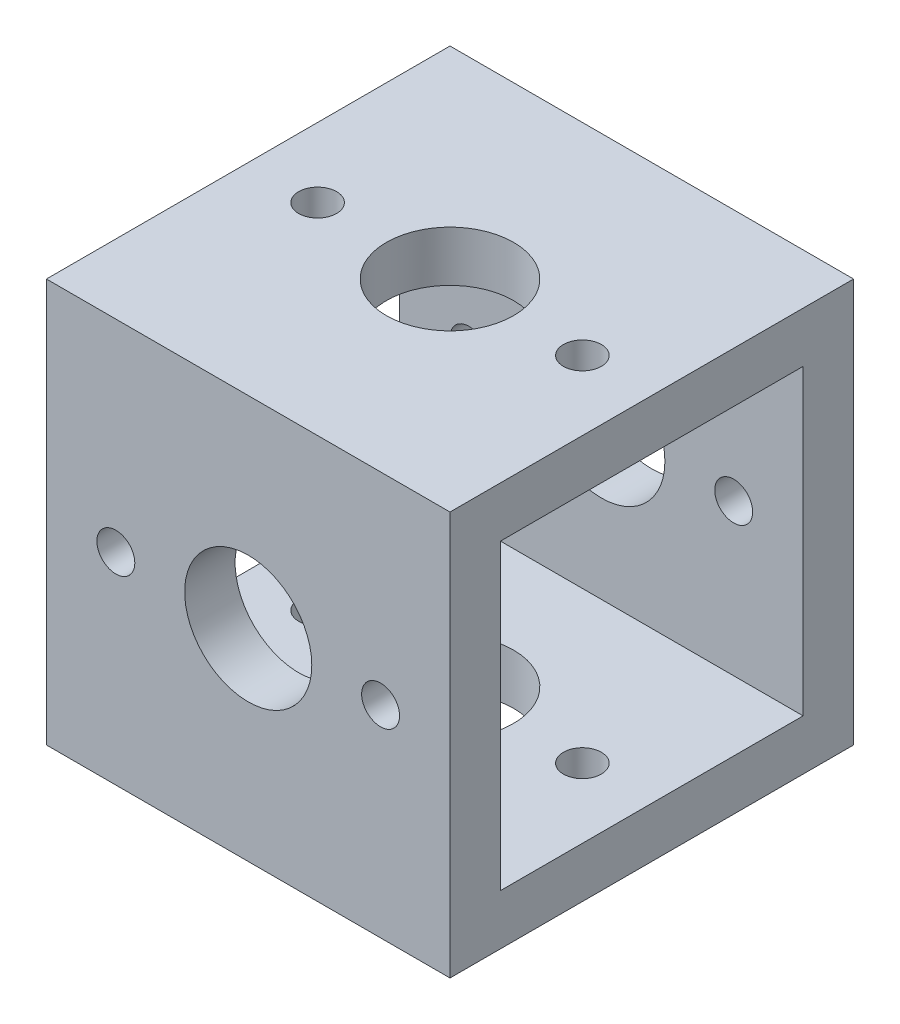
SolidWorks part; units mm, degrees
ref_plane "Front" through (0, 0, 0) normal (0, 0, 1) x (1, 0, 0)
ref_plane "Top" through (0, 0, 0) normal (0, 1, 0) x (1, 0, 0)
ref_plane "Right" through (0, 0, 0) normal (1, 0, 0) x (0, 0, -1)
sketch "Sketch1" plane through (0, 0, 0) normal (1, 0, 0) x (0, 0, -1)
  line L0 (-24.6126, -0.7874) -> (-24.6126, 24.6126)
  line L1 (-2.3876, 2.3876) -> (-21.4376, 2.3876)
  line L2 (-21.4376, 2.3876) -> (-21.4376, 21.4376)
  line L3 (-2.3876, 21.4376) -> (-21.4376, 21.4376)
  line L4 (-2.3876, 2.3876) -> (-2.3876, 21.4376)
  line L5 (0.7874, 24.6126) -> (-24.6126, 24.6126)
  line L6 (0.7874, -0.7874) -> (0.7874, 24.6126)
  line L7 (0.7874, -0.7874) -> (-24.6126, -0.7874)
  dimension "D1" = 3.175
extrude "Extrude1" add sketch "Sketch1" along normal blind 25.4
sketch "Sketch2" plane through (0, 0, 0) normal (0, 0, 1) x (1, 0, 0)
  line L2 (0, 11.9126) -> (12.7, 11.9126)
  line L3 (0, -0.7874) -> (0, 24.6126) construction
  circle A7 centre (4.3688, 11.9126) radius 1.1938
  circle A8 centre (21.0312, 11.9126) radius 1.1938
  circle A11 centre (12.7, 11.9126) radius 4.0005
sketch "Sketch3" plane through (0, 0, 0) normal (0, 1, 0) x (1, 0, 0)
  circle A5 centre (12.7, -11.9126) radius 4.0005
  circle A8 centre (4.3688, -11.9126) radius 1.1938
  circle A9 centre (21.0312, -11.9126) radius 1.1938
extrude "Cut-Extrude1" cut sketch "Sketch3" along normal through all and the other way blind 25.4
extrude "Cut-Extrude2" cut sketch "Sketch2" along normal through all and the other way blind 25.4
